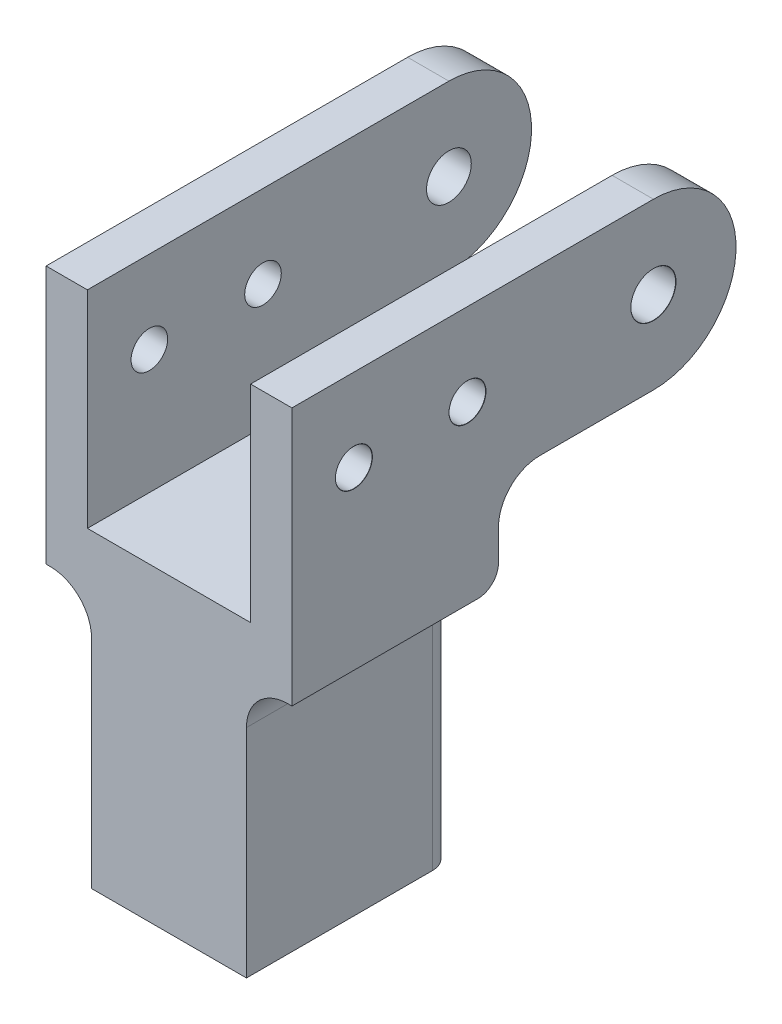
SolidWorks part; units mm, degrees
ref_plane "Front Plane" through (0, 0, 0) normal (0, 0, 1) x (1, 0, 0)
ref_plane "Top Plane" through (0, 0, 0) normal (0, 1, 0) x (1, 0, 0)
ref_plane "Right Plane" through (0, 0, 0) normal (1, 0, 0) x (0, 0, -1)
sketch "Sketch1" plane through (0, 0, 0) normal (0, 0, 1) x (1, 0, 0)
  line L14 (0, 15.1837) -> (0, -65.9837) construction
  line L15 (-15.113, 0) -> (-10.033, 0)
  line L16 (-10.033, 0) -> (-10.033, -25.4)
  line L17 (-10.033, -25.4) -> (10.033, -25.4)
  line L18 (-15.113, 0) -> (-15.113, -31.75)
  line L19 (-15.113, -31.75) -> (-9.525, -31.75)
  line L20 (-9.525, -31.75) -> (-9.525, -63.5)
  line L21 (-9.525, -63.5) -> (9.525, -63.5)
  line L22 (9.525, -31.75) -> (9.525, -63.5)
  line L23 (15.113, -31.75) -> (9.525, -31.75)
  line L24 (15.113, 0) -> (15.113, -31.75)
  line L25 (10.033, 0) -> (10.033, -25.4)
  line L26 (15.113, 0) -> (10.033, 0)
  point P3 (-12.573, 0)
  point P11 (0, -65.9837)
  point P13 (0, -63.5)
  point P18 (0, -25.4)
  dimension "D1" = 20.066
  dimension "D2" = 5.08
  dimension "D3" = 25.4
  dimension "D4" = 6.35
  dimension "D5" = 31.75
  dimension "D6" = 19.05
extrude "Boss-Extrude1" add sketch "Sketch1" along normal blind 25.4
sketch "Sketch2" plane through (0, -63.5, 0) normal (0, -1, 0) x (1, 0, 0)
  line L0 (9.525, 25.4) -> (9.525, 0) construction
  line L1 (-6.35, 22.86) -> (6.35, 22.86)
  line L2 (-6.35, 22.86) -> (-6.35, 10.16)
  line L3 (-6.35, 10.16) -> (6.35, 10.16)
  line L4 (6.35, 22.86) -> (6.35, 10.16)
  line L5 (-9.525, 25.4) -> (9.525, 25.4) construction
  line L7 (-6.35, 2.54) -> (6.35, 2.54)
  line L8 (-6.35, 2.54) -> (-6.35, 7.62)
  line L9 (-6.35, 7.62) -> (6.35, 7.62)
  line L10 (6.35, 2.54) -> (6.35, 7.62)
  point P10 (0, 25.4)
  point P11 (0, 22.86)
  dimension "D1" = 12.7
  dimension "D2" = 12.7
  dimension "D3" = 2.54
  dimension "D4" = 5.08
  dimension "D5" = 2.54
extrude "Cut-Extrude1" cut sketch "Sketch2" against normal blind 31.75
hole_wizard "M4 Clearance Hole4" positions "Sketch3" profile "Sketch5" hole size "M4" standard "ANSI Metric"
sketch "Sketch3" plane through (0, 0, 0) normal (0, 0, -1) x (-1, 0, 0)
  line L0 (9.525, -63.5) -> (-9.525, -63.5) construction
  point P0 (0, -57.15)
  point P2 (0, -45.72)
  dimension "D1" = 11.43
  dimension "D2" = 6.35
sketch "Sketch5" plane through (0, -57.15, 0) normal (1, 0, 0) x (0, 1, 0)
  line L0 (0, 0) -> (0, 11.5119)
  line L1 (0, 11.5119) -> (2.25, 10.16)
  line L2 (2.25, 10.16) -> (2.25, 0.021)
  line L3 (2.25, 0.021) -> (2.275, 0)
  line L5 (2.275, 0) -> (0, 0)
  line L6 (-2.25, 0.021) -> (-2.275, 0) construction
  line L10 (0, 11.5119) -> (-2.25, 10.16) construction
  line L11 (0, -6.35) -> (0, 107.95) construction
  dimension "Hole Dia." = 4.5
  dimension "Hole Depth" = 10.16
  dimension "Near C'Sink Dia." = 4.55
  dimension "Near C'Sink Angle" = 100
  dimension "Drill Angle" = 118
sketch "Sketch6" plane through (0, 0, 0) normal (0, 0, -1) x (-1, 0, 0)
  line L0 (-10.033, 0) -> (-10.033, -25.4) construction
  line L1 (-15.113, 0) -> (-10.033, 0)
  line L2 (-15.113, 0) -> (-15.113, -20.32)
  line L3 (-15.113, -20.32) -> (-10.033, -20.32)
  line L4 (-10.033, 0) -> (-10.033, -20.32)
  line L5 (0, 11.9044) -> (0, -79.0787) construction
  line L6 (10.033, 0) -> (10.033, -20.32)
  line L7 (15.113, -20.32) -> (10.033, -20.32)
  line L8 (15.113, 0) -> (15.113, -20.32)
  line L9 (15.113, 0) -> (10.033, 0)
  dimension "0.8" = 20.32
extrude "Boss-Extrude2" add sketch "Sketch6" along normal blind 19.05
sketch "Sketch7" plane through (15.113, 0, 0) normal (1, 0, 0) x (0, 0, -1)
  line L0 (19.05, 0) -> (19.05, -20.32) construction
  line L1 (19.05, -20.32) -> (19.05, 0)
  arc A0 (19.05, 0) -> (19.05, -20.32) centre (19.05, -10.16) cw
extrude "Boss-Extrude3" add sketch "Sketch7" against normal up to surface (5.08 mm away) up to face at (10.033, -15.24, 2.1167)
sketch "Sketch8" plane through (-15.113, 0, 0) normal (-1, 0, 0) x (0, 0, 1)
  line L0 (-19.05, -20.32) -> (-19.05, 0) construction
  line L1 (-19.05, -20.32) -> (0, -20.32) construction
  line L2 (-19.05, -20.32) -> (-19.05, 0)
  arc A0 (-19.05, 0) -> (-19.05, -20.32) centre (-19.05, -10.16) ccw
extrude "Boss-Extrude4" add sketch "Sketch8" against normal up to surface (5.08 mm away) up to face at (-10.033, -15.24, 2.1167)
hole_wizard "M4 Clearance Hole5" positions "Sketch9" profile "Sketch10" hole size "M4" standard "ANSI Metric"
sketch "Sketch9" plane through (15.113, 0, 0) normal (1, 0, 0) x (0, 0, -1)
  line L0 (19.05, 0) -> (19.05, -20.32) construction
  line L2 (-25.4, -31.75) -> (-25.4, 0) construction
  point P0 (-17.78, -10.16)
  point P2 (-3.81, -10.16)
  point P14 (19.05, -10.16)
  dimension "D1" = 13.97
  dimension "D2" = 7.62
sketch "Sketch10" plane through (15.113, -10.16, 17.78) normal (0, 1, 0) x (0, 0, -1)
  line L0 (0, 0) -> (0, 31.5779)
  line L1 (0, 31.5779) -> (2.25, 30.226)
  line L2 (2.25, 30.226) -> (2.25, 0.021)
  line L3 (2.25, 0.021) -> (2.275, 0)
  line L5 (2.275, 0) -> (0, 0)
  line L6 (-2.25, 0.021) -> (-2.275, 0) construction
  line L10 (0, 31.5779) -> (-2.25, 30.226) construction
  line L11 (0, -6.35) -> (0, 107.95) construction
  dimension "Hole Dia." = 4.5
  dimension "Hole Depth" = 30.226
  dimension "Near C'Sink Dia." = 4.55
  dimension "Near C'Sink Angle" = 100
  dimension "Drill Angle" = 118
hole_wizard "M5 Clearance Hole1" positions "Sketch13" profile "Sketch14" hole size "M5" standard "ANSI Metric"
sketch "Sketch13" plane through (15.113, 0, 0) normal (1, 0, 0) x (0, 0, -1)
  line L0 (19.05, 0) -> (19.05, -20.32) construction
  point P0 (19.05, -10.16)
  point P9 (19.05, -10.16)
sketch "Sketch14" plane through (15.113, -10.16, -19.05) normal (0, 1, 0) x (0, 0, -1)
  line L0 (0, 0) -> (0, 31.8784)
  line L1 (0, 31.8784) -> (2.75, 30.226)
  line L2 (2.75, 30.226) -> (2.75, 0.021)
  line L3 (2.75, 0.021) -> (2.775, 0)
  line L5 (2.775, 0) -> (0, 0)
  line L6 (-2.75, 0.021) -> (-2.775, 0) construction
  line L10 (0, 31.8784) -> (-2.75, 30.226) construction
  line L11 (0, -6.35) -> (0, 107.95) construction
  dimension "Hole Dia." = 5.5
  dimension "Hole Depth" = 30.226
  dimension "Near C'Sink Dia." = 5.55
  dimension "Near C'Sink Angle" = 100
  dimension "Drill Angle" = 118
fillet "Fillet1" radius 5.08 4 edges at (12.573, -20.32, 0) (-12.573, -20.32, 0) (-9.525, -31.75, 12.7) (9.525, -31.75, 12.7)
fillet "Fillet2" radius 2.54 6 edges at (-14.859, -31.75, 0) (-11.0129, -33.2379, 0) (14.859, -31.75, 0) (11.0129, -33.2379, 0) (-9.525, -50.165, 0) (9.525, -50.165, 0)
